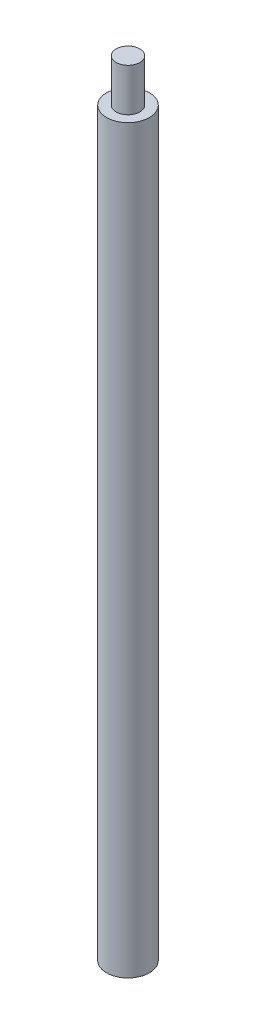
SolidWorks part; units mm, degrees
ref_plane "Front Plane" through (0, 0, 0) normal (0, 0, 1) x (1, 0, 0)
ref_plane "Top Plane" through (0, 0, 0) normal (0, 1, 0) x (1, 0, 0)
ref_plane "Right Plane" through (0, 0, 0) normal (1, 0, 0) x (0, 0, -1)
sketch "Sketch1" plane through (0, 0, 0) normal (0, 1, 0) x (1, 0, 0)
  circle A0 centre (0, 0) radius 3.175
  dimension "D1" = 6.35
extrude "Boss-Extrude1" add sketch "Sketch1" along normal blind 109.728
hole_wizard "#6-32 Tapped Hole1" positions "Sketch2" profile "Sketch3" tap size "#6-32" standard "ANSI Inch"
sketch "Sketch2" plane through (0, 0, 0) normal (0, -1, 0) x (-1, 0, 0)
  point P0 (0, 0)
sketch "Sketch3" plane through (0, 0, 0) normal (1, 0, 0) x (0, 0, -1)
  line L0 (0, 0) -> (0, 10.2107)
  line L1 (0, 10.2107) -> (1.3525, 9.398)
  line L2 (1.3525, 9.398) -> (1.3525, 7.112)
  line L3 (1.3525, 7.112) -> (1.7526, 7.112)
  line L4 (1.7526, 7.112) -> (1.7526, 0)
  line L5 (1.7526, 0) -> (0, 0)
  line L10 (0, 10.2107) -> (-1.3526, 9.398) construction
  line L11 (0, -6.35) -> (0, 107.95) construction
  dimension "Tap Drill Dia." = 2.7051
  dimension "Tap Drill Depth" = 9.398
  dimension "Thread Major Dia." = 3.5052
  dimension "Thread Depth" = 7.112
  dimension "Drill Angle" = 118
sketch "Sketch4" plane through (0, 109.728, 0) normal (0, 1, 0) x (1, 0, 0)
  circle A0 centre (0, 0) radius 1.7526
  dimension "D1" = 3.5052
extrude "Boss-Extrude2" add sketch "Sketch4" along normal blind 6.35
cosmetic thread "Cosmetic Thread1" parameters "D2"=2.5603
